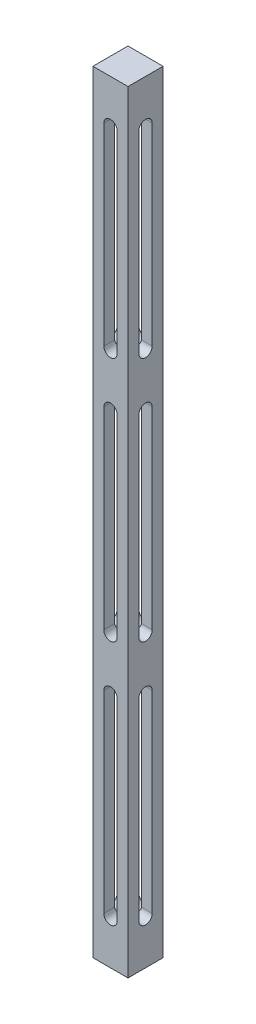
SolidWorks part; units mm, degrees
material "6061-T6 (SS)"
ref_plane "Front Plane" through (0, 0, 0) normal (0, 0, 1) x (1, 0, 0)
ref_plane "Top Plane" through (0, 0, 0) normal (0, 1, 0) x (1, 0, 0)
ref_plane "Right Plane" through (0, 0, 0) normal (1, 0, 0) x (0, 0, -1)
sketch "Sketch1" plane through (0, 0, 0) normal (0, 1, 0) x (1, 0, 0)
  line L1 (-6.35, -6.35) -> (6.35, -6.35)
  line L2 (-6.35, -6.35) -> (-6.35, 6.35)
  line L3 (-6.35, 6.35) -> (6.35, 6.35)
  line L4 (6.35, -6.35) -> (6.35, 6.35)
  line L5 (-6.35, -6.35) -> (6.35, 6.35) construction
  line L6 (-6.35, 6.35) -> (6.35, -6.35) construction
  point P0 (0, 0)
  dimension "D1" = 12.7
  dimension "D2" = 12.7
extrude "Boss-Extrude1" add sketch "Sketch1" along normal blind 279.4
sketch "Sketch2" plane through (0, 0, -6.35) normal (0, 0, -1) x (-1, 0, 0)
  line L0 (-6.35, 279.4) -> (6.35, 279.4) construction
  line L1 (-2.413, 263.525) -> (-2.413, 193.675)
  line L2 (2.413, 263.525) -> (2.413, 193.675)
  arc A0 (2.413, 263.525) -> (-2.413, 263.525) centre (0, 263.525) ccw
  arc A2 (-2.413, 193.675) -> (2.413, 193.675) centre (0, 193.675) ccw
  dimension "D1" = 15.875
  dimension "D2" = 2.413
  dimension "D3" = 69.85
extrude "Cut-Extrude1" cut sketch "Sketch2" against normal through all
sketch "Sketch3" plane through (6.35, 0, 0) normal (1, 0, 0) x (0, 0, -1)
  line L0 (-2.413, 263.525) -> (-2.413, 193.675)
  line L1 (2.413, 263.525) -> (2.413, 193.675)
  line L2 (-6.35, 279.4) -> (6.35, 279.4) construction
  line L3 (6.35, 279.4) -> (6.35, 0) construction
  arc A0 (2.413, 263.525) -> (-2.413, 263.525) centre (0, 263.525) ccw
  arc A1 (-2.413, 193.675) -> (2.413, 193.675) centre (0, 193.675) ccw
  dimension "D4" = 2.413
  dimension "D1" = 15.875
  dimension "D2" = 69.85
  dimension "D3" = 6.35
extrude "Cut-Extrude2" cut sketch "Sketch3" against normal through all
pattern_linear "LPattern1" count 3 spacing 88.9 along (0, -1, 0) of "Cut-Extrude1", "Cut-Extrude2"
